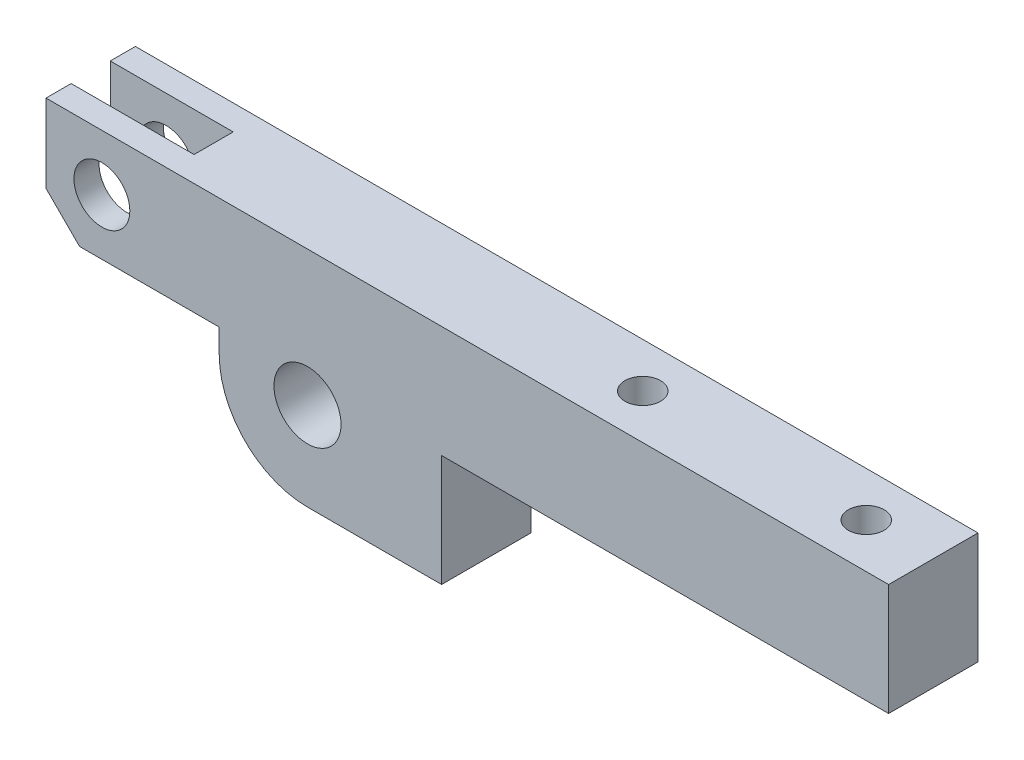
SolidWorks part; units mm, degrees
ref_plane "Face" through (0, 0, 0) normal (0, 0, 1) x (1, 0, 0)
ref_plane "Dessus" through (0, 0, 0) normal (0, 1, 0) x (1, 0, 0)
ref_plane "Droite" through (0, 0, 0) normal (1, 0, 0) x (0, 0, -1)
sketch "Esquisse1" plane through (0, 0, 0) normal (0, 0, 1) x (1, 0, 0)
  line L0 (-23.4, 12.1) -> (52, 12.1)
  line L1 (52, 12.1) -> (52, 2.1)
  line L2 (52, 2.1) -> (12, 2.1)
  line L3 (12, 2.1) -> (12, -7.9)
  line L4 (12, -7.9) -> (0, -7.9)
  line L5 (-7.9, 2.1) -> (-23.4, 2.1)
  line L6 (-23.4, 2.1) -> (-23.4, 12.1)
  line L7 (-7.9, 0) -> (-7.9, 2.1)
  circle A0 centre (0, 0) radius 3
  circle A1 centre (-18.4, 7.1) radius 2.5
  arc A2 (0, -7.9) -> (-7.9, 0) centre (0, 0) cw
  dimension "D1" = 6
  dimension "D2" = 5
  dimension "D3" = 18.4
  dimension "D4" = 7.1
  dimension "D9" = 5
  dimension "D11" = 7.9
  dimension "D5" = 5
  dimension "D6" = 75.4
  dimension "D7" = 40
  dimension "D8" = 10
  dimension "D10" = 10
extrude "Base-Extrusion" add sketch "Esquisse1" along normal mid plane 8
chamfer "Chanfrein1" distance 3 angle 45 1 edges at (-23.4, 2.1, 0)
sketch "Esquisse2" plane through (0, 0, 0) normal (0, 0, 1) x (1, 0, 0)
  line L0 (-12.4, 12.1) -> (-12.4, 2.1)
  line L1 (52, 12.1) -> (-23.4, 12.1) construction
  line L2 (-20.4, 2.1) -> (-7.9, 2.1) construction
  line L11 (-23.4, 12.1) -> (-23.4, 5.1)
  line L12 (-20.4, 2.1) -> (-7.9, 2.1)
  line L13 (-7.9, 2.1) -> (-7.9, 0)
  line L14 (0, -7.9) -> (12, -7.9)
  line L15 (12, -7.9) -> (12, 2.1)
  line L16 (12, 2.1) -> (52, 2.1)
  line L17 (52, 2.1) -> (52, 12.1)
  line L18 (52, 12.1) -> (-23.4, 12.1)
  line L19 (-23.4, 12.1) -> (-23.4, 5.1)
  line L20 (-20.4, 2.1) -> (-12.4, 2.1)
  line L22 (-23.4, 5.1) -> (-20.4, 2.1)
  line L23 (-23.4, 5.1) -> (-20.4, 2.1)
  line L26 (-12.4, 12.1) -> (-23.4, 12.1)
  circle A0 centre (-18.4, 7.1) radius 2.5 construction
  arc A1 (-7.9, 0) -> (0, -7.9) centre (0, 0) ccw
  dimension "D2" = 6
  dimension "D1" = 0
extrude "Enlèv. mat.-Extru.2" cut sketch "Esquisse2" against normal mid plane 3.5
sketch "Esquisse7" plane through (0, 12.1, 0) normal (0, 1, 0) x (-1, 0, 0)
  line L0 (-52, 0) -> (-26, 0) construction
  line L1 (-52, 4) -> (-52, -4) construction
  circle A0 centre (-46, 0) radius 1.6
  circle A1 centre (-26, 0) radius 1.6
  dimension "D1" = 3.2
  dimension "D2" = 26
  dimension "D3" = 20
extrude "Enlèv. mat.-Extru.3" cut sketch "Esquisse7" against normal through all
cosmetic thread "Représentation de filetage1" parameters "D2"=4
cosmetic thread "Représentation de filetage2" parameters "D2"=4
sketch "Point doigt" plane through (0, 2.1, 0) normal (0, -1, 0) x (1, 0, 0)
  point P0 (32.9294, 0)
  dimension "D1" = 35
